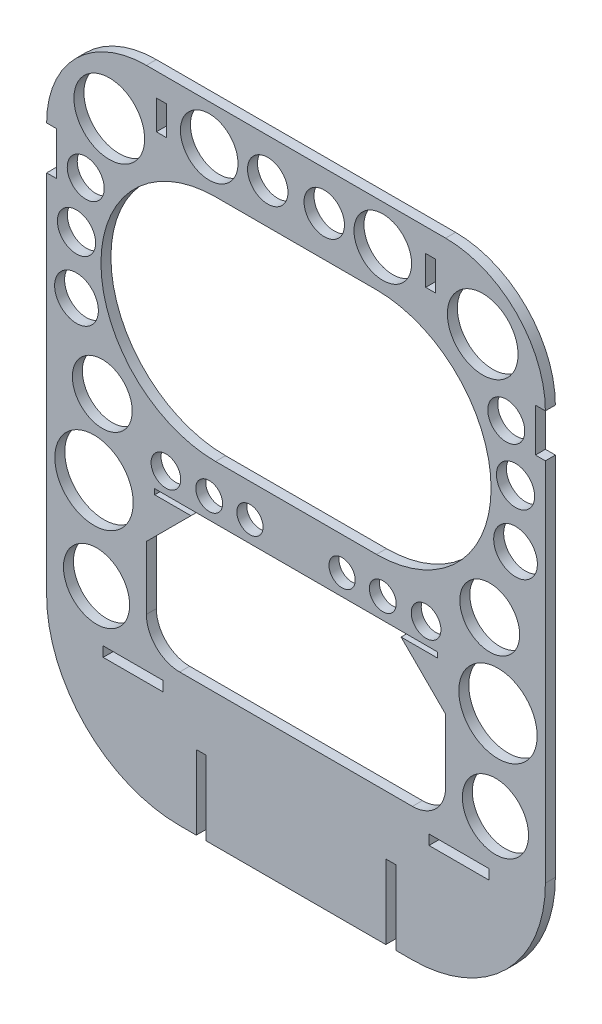
SolidWorks part; units mm, degrees
ref_plane "Front Plane" through (0, 0, 0) normal (0, 0, 1) x (1, 0, 0)
ref_plane "Top Plane" through (0, 0, 0) normal (0, 1, 0) x (1, 0, 0)
ref_plane "Right Plane" through (0, 0, 0) normal (1, 0, 0) x (0, 0, -1)
sketch "Sketch1" plane through (0, 0, 0) normal (0, 0, 1) x (1, 0, 0)
  line L0 (0, 96.5) -> (0, -96.5) construction
  line L1 (-75, 96.5) -> (75, 96.5) construction
  line L2 (-75, 96.5) -> (-75, -96.5) construction
  line L3 (-75, -96.5) -> (75, -96.5) construction
  line L4 (75, 96.5) -> (75, -96.5) construction
  line L5 (-45, 96.5) -> (45, 96.5)
  line L6 (-35, -96.5) -> (35, -96.5) construction
  line L7 (-75, 66.5) -> (75, 66.5) construction
  line L8 (-75, 66.5) -> (-75, -56.5)
  line L9 (-75, -56.5) -> (75, -56.5) construction
  line L10 (75, 66.5) -> (75, -56.5)
  line L11 (-0.5, -96.5) -> (0.5, -96.5) construction
  line L12 (-35, -96.5) -> (-0.5, -96.5)
  line L13 (0.5, -96.5) -> (35, -96.5)
  line L14 (-0.5, -96.5) -> (0.5, -96.5)
  arc A0 (-75, 66.5) -> (-45, 96.5) centre (-45, 66.5) cw
  arc A1 (45, 96.5) -> (75, 66.5) centre (45, 66.5) cw
  arc A2 (-75, -56.5) -> (-35, -96.5) centre (-35, -56.5) ccw
  arc A3 (35, -96.5) -> (75, -56.5) centre (35, -56.5) ccw
  point P10 (0, 96.5)
  point P19 (0, -96.5)
  point P23 (0, -96.5)
  dimension "D3" = 40
  dimension "D4" = 30
  dimension "D1" = 193
  dimension "D2" = 150
  dimension "D5" = 1
  dimension "D6" = 96.5
extrude "Boss-Extrude1" add sketch "Sketch1" along normal blind 3
sketch "Sketch2" plane through (0, 0, 3) normal (0, 0, 1) x (1, 0, 0)
  line L0 (0, -1.65) -> (0, 1.65) construction
  line L1 (-38, -56.5) -> (38, -56.5) construction
  line L2 (-45, -49.5) -> (-45, -19.5) construction
  line L3 (-38, -12.5) -> (38, -12.5) construction
  line L4 (45, -49.5) -> (45, -19.5) construction
  line L5 (-45, -56.5) -> (45, -12.5) construction
  line L6 (-45, -12.5) -> (45, -56.5) construction
  line L7 (-35, -96.5) -> (35, -96.5) construction
  line L9 (-45, -56.5) -> (45, -56.5)
  line L10 (-45, -56.5) -> (-45, -12.5)
  line L11 (-45, -12.5) -> (45, -12.5)
  line L12 (45, -56.5) -> (45, -12.5)
  line L13 (-45, -56.5) -> (45, -12.5) construction
  line L14 (-45, -12.5) -> (45, -56.5) construction
  arc A0 (38, -56.5) -> (45, -49.5) centre (38, -49.5) ccw construction
  arc A1 (38, -12.5) -> (45, -19.5) centre (38, -19.5) cw construction
  arc A2 (-45, -19.5) -> (-38, -12.5) centre (-38, -19.5) cw construction
  arc A3 (-38, -56.5) -> (-45, -49.5) centre (-38, -49.5) cw construction
  point P0 (0, -34.5)
  point P21 (0, -34.5)
  dimension "D4" = 7
  dimension "D1" = 84
  dimension "D2" = 40
  dimension "D3" = 90
extrude "Cut-Extrude1" cut sketch "Sketch2" against normal blind 10
fillet "Fillet1" radius 10 2 edges at (45, -56.5, 1.5) (-45, -56.5, 1.5)
chamfer "Chamfer1" distance 15 angle 45 2 edges at (45, -12.5, 1.5) (-45, -12.5, 1.5)
sketch "Sketch3" plane through (0, 0, 0) normal (0, 0, -1) x (-1, 0, 0)
  line L0 (0, 1.65) -> (0, -1.65) construction
  line L1 (-42.5, -14.1) -> (42.5, -14.1)
  line L2 (-42.5, -14.1) -> (-42.5, -12.5)
  line L3 (-42.5, -12.5) -> (42.5, -12.5)
  line L4 (42.5, -14.1) -> (42.5, -12.5)
  line L5 (-42.5, -14.1) -> (42.5, -12.5) construction
  line L6 (-42.5, -12.5) -> (42.5, -14.1) construction
  line L7 (30, -12.5) -> (-30, -12.5) construction
  point P0 (0, -13.3)
  dimension "D1" = 1.6
  dimension "D2" = 85
extrude "Cut-Extrude2" cut sketch "Sketch3" against normal blind 10
sketch "Sketch5" plane through (0, 0, 0) normal (0, 0, -1) x (-1, 0, 0)
  line L0 (-75, -56.5) -> (-75, 66.5) construction
  line L1 (-75, 66.5) -> (-72, 66.5)
  line L2 (-75, 66.5) -> (-75, 53.5)
  line L3 (-75, 53.5) -> (-72, 53.5)
  line L4 (-72, 66.5) -> (-72, 53.5)
  line L5 (0, 1.65) -> (0, -1.65) construction
  line L6 (-42, 89.5) -> (-39, 89.5)
  line L7 (-42, 89.5) -> (-42, 80.68)
  line L8 (-42, 80.68) -> (-39, 80.68)
  line L9 (-39, 89.5) -> (-39, 80.68)
  line L10 (75, 53.5) -> (72, 53.5)
  line L11 (72, 66.5) -> (72, 53.5)
  line L12 (75, 66.5) -> (72, 66.5)
  line L13 (75, 66.5) -> (75, 53.5)
  line L14 (42, 80.68) -> (39, 80.68)
  line L15 (39, 89.5) -> (39, 80.68)
  line L16 (42, 89.5) -> (39, 89.5)
  line L17 (42, 89.5) -> (42, 80.68)
  line L18 (-45, 96.5) -> (45, 96.5) construction
  line L19 (35, -96.5) -> (-35, -96.5) construction
  line L20 (-58, -61.19) -> (-40, -61.19)
  line L21 (-58, -61.19) -> (-58, -64.19)
  line L22 (-58, -64.19) -> (-40, -64.19)
  line L23 (-40, -61.19) -> (-40, -64.19)
  line L24 (58, -64.19) -> (40, -64.19)
  line L25 (40, -61.19) -> (40, -64.19)
  line L26 (58, -61.19) -> (40, -61.19)
  line L27 (58, -61.19) -> (58, -64.19)
  line L28 (30, -74.19) -> (27, -74.19)
  line L29 (-30, -96.5) -> (-27, -96.5)
  line L30 (-30, -96.5) -> (-30, -74.19)
  line L31 (-30, -74.19) -> (-27, -74.19)
  line L32 (-27, -96.5) -> (-27, -74.19)
  line L33 (27, -96.5) -> (27, -74.19)
  line L34 (30, -96.5) -> (27, -96.5)
  line L35 (30, -96.5) -> (30, -74.19)
  dimension "D1" = 3
  dimension "D2" = 3
  dimension "D3" = 7
  dimension "D4" = 8.82
  dimension "D5" = 78
  dimension "D6" = 30
  dimension "D7" = 13
  dimension "D8" = 3
  dimension "D9" = 18
  dimension "D10" = 35.31
  dimension "D11" = 40
  dimension "D12" = 30
  dimension "D13" = 3
  dimension "D14" = 22.31
extrude "Cut-Extrude3" cut sketch "Sketch5" against normal blind 10
sketch "Sketch6" plane through (0, 0, 0) normal (0, 0, -1) x (-1, 0, 0)
  line L0 (-24.2127, 38.1852) -> (24.2127, 38.1852) construction
  line L1 (-24.2127, 72.638) -> (24.2127, 72.638)
  line L2 (-24.2127, 3.7324) -> (24.2127, 3.7324)
  line L3 (0, 1.65) -> (0, -1.65) construction
  arc A0 (-24.2127, 72.638) -> (-24.2127, 3.7324) centre (-24.2127, 38.1852) ccw
  arc A1 (24.2127, 3.7324) -> (24.2127, 72.638) centre (24.2127, 38.1852) ccw
  point P2 (0, 38.1852)
extrude "Cut-Extrude4" cut sketch "Sketch6" against normal blind 10
sketch "Sketch7" plane through (0, 0, 0) normal (0, 0, -1) x (-1, 0, 0)
  line L1 (0, 1.65) -> (0, -1.65) construction
  circle A0 centre (-56.1555, 77.0403) radius 10.6311
  circle A1 centre (-26.105, 84.6964) radius 8.662
  circle A2 centre (-63.2375, 58.0912) radius 5.5639
  circle A3 centre (-66.021, 42.5875) radius 5.7438
  circle A4 centre (-66.021, 25.3611) radius 6.5751
  circle A5 centre (-58.261, 4.3066) radius 8.998
  circle A6 centre (-60.7492, -19.4275) radius 11.7881
  circle A7 centre (-59.9836, -46.607) radius 9.9549
  circle A12 centre (-8.4958, 84.6964) radius 6.0829
  circle A13 centre (-39.1205, -6.2206) radius 4.4643
  circle A14 centre (-26.105, -6.2206) radius 4.0377
  circle A15 centre (-13.8552, -6.2206) radius 3.9459
  circle A16 centre (13.8552, -6.2206) radius 3.9459
  circle A17 centre (26.105, -6.2206) radius 4.0377
  circle A18 centre (39.1205, -6.2206) radius 4.4643
  circle A19 centre (8.4958, 84.6964) radius 6.0829
  circle A24 centre (59.9836, -46.607) radius 9.9549
  circle A25 centre (60.7492, -19.4275) radius 11.7881
  circle A26 centre (58.261, 4.3066) radius 8.998
  circle A27 centre (66.021, 25.3611) radius 6.5751
  circle A28 centre (66.021, 42.5875) radius 5.7438
  circle A29 centre (63.2375, 58.0912) radius 5.5639
  circle A30 centre (26.105, 84.6964) radius 8.662
  circle A31 centre (56.1555, 77.0403) radius 10.6311
extrude "Cut-Extrude5" cut sketch "Sketch7" against normal blind 10
